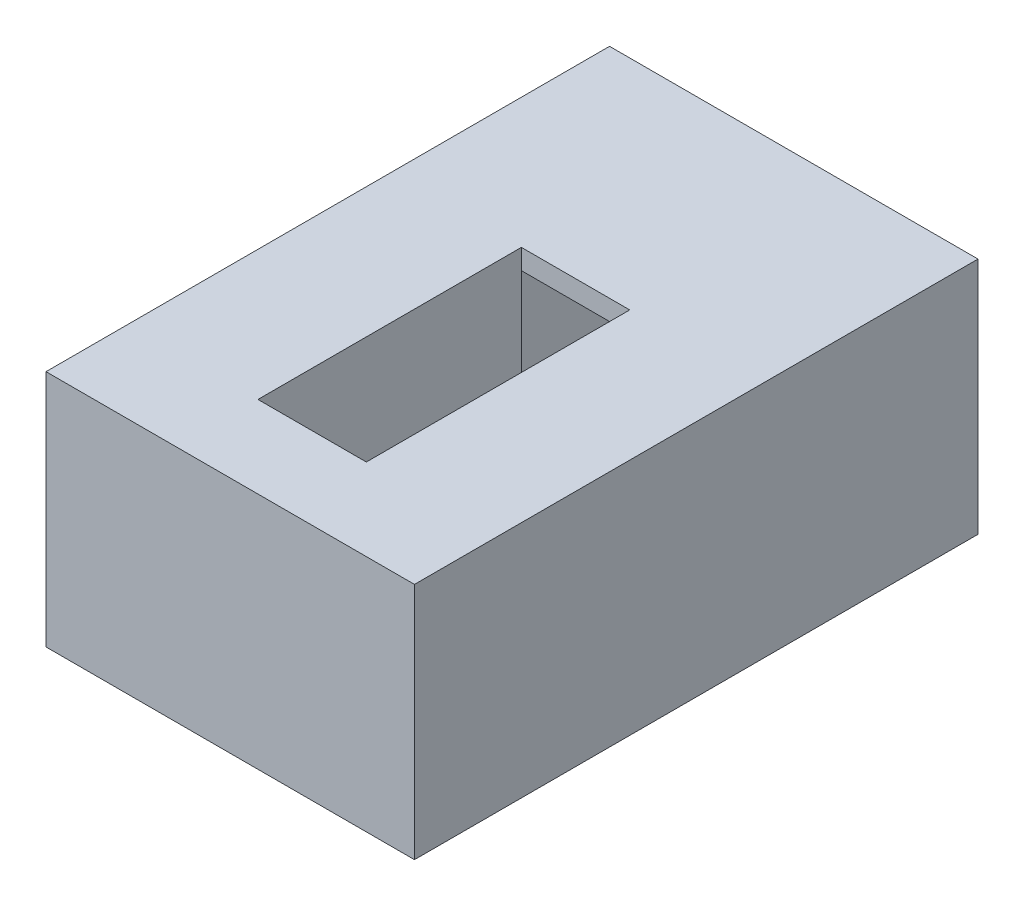
SolidWorks part; units mm, degrees
ref_plane "Спереди" through (0, 0, 0) normal (0, 0, 1) x (1, 0, 0)
ref_plane "Сверху" through (0, 0, 0) normal (0, 1, 0) x (1, 0, 0)
ref_plane "Справа" through (0, 0, 0) normal (1, 0, 0) x (0, 0, -1)
sketch "Эскиз1" plane through (0, 0, 0) normal (1, 0, 0) x (0, 0, -1)
  line L1 (-2600, 1100) -> (2600, 1100)
  line L2 (-2600, 1100) -> (-2600, -1100)
  line L3 (-2600, -1100) -> (2600, -1100)
  line L4 (2600, 1100) -> (2600, -1100)
  line L5 (-2600, 1100) -> (2600, -1100) construction
  line L6 (-2600, -1100) -> (2600, 1100) construction
  point P0 (0, 0)
extrude "Бобышка-Вытянуть1" add sketch "Эскиз1" along normal mid plane 3400
sketch "Эскиз3" plane through (0, 0, 0) normal (1, 0, 0) x (0, 0, -1)
  line L0 (-1844.1325, 930.2672) -> (-2363.5134, 930.2672)
  line L1 (-2363.5134, 930.2672) -> (-2363.5134, -219.7328)
  line L2 (-2363.5134, -219.7328) -> (586.4866, -219.7328)
  line L3 (586.4866, -219.7328) -> (586.4866, -780.2687)
  line L4 (586.4866, -780.2687) -> (2386.4866, -780.2687)
  line L5 (2386.4866, -780.2687) -> (2386.4866, 914.3685)
  line L6 (2386.4866, 914.3685) -> (586.4866, 914.3685)
  line L8 (-1844.1325, 930.2672) -> (-1844.1325, 1100)
  line L9 (2600, 1100) -> (-2600, 1100) construction
  line L10 (-1844.1325, 1100) -> (586.4866, 1100)
  line L11 (586.4866, 1100) -> (586.4866, 914.3685)
  dimension "D1" = 1800
  dimension "D2" = 4750
  dimension "D3" = 1150
  dimension "D4" = 1800
extrude "Вырез-Вытянуть1" cut sketch "Эскиз3" against normal mid plane 1000
sketch "Эскиз4" plane through (0, 0, 0) normal (1, 0, 0) x (0, 0, -1)
  line L0 (2386.4866, 914.3685) -> (586.4866, 914.3685) construction
  line L1 (2386.4866, 914.3685) -> (586.4866, 914.3685)
  line L2 (2386.4866, 914.3685) -> (2386.4866, -780.2687)
  line L3 (2386.4866, -780.2687) -> (586.4866, -780.2687)
  line L4 (586.4866, 914.3685) -> (586.4866, -780.2687)
  line L5 (2386.4866, -780.2687) -> (2386.4866, 914.3685) construction
extrude "Вырез-Вытянуть2" cut sketch "Эскиз4" against normal mid plane 2000
